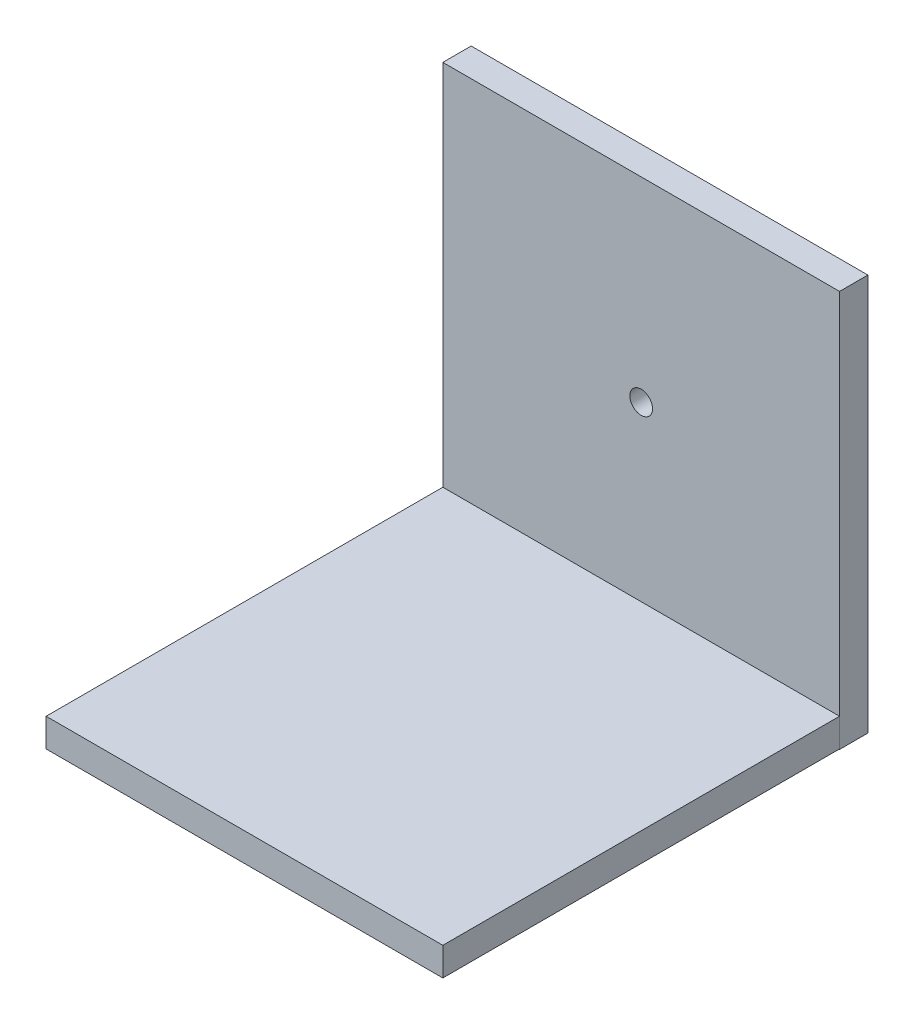
SolidWorks part; units mm, degrees
ref_plane "Front Plane" through (0, 0, 0) normal (0, 0, 1) x (1, 0, 0)
ref_plane "Top Plane" through (0, 0, 0) normal (0, 1, 0) x (1, 0, 0)
ref_plane "Right Plane" through (0, 0, 0) normal (1, 0, 0) x (0, 0, -1)
sketch "Sketch1" plane through (0, 0, 0) normal (0, 1, 0) x (1, 0, 0)
  line L1 (0, 0) -> (70, 0)
  line L2 (0, 0) -> (0, -70)
  line L3 (0, -70) -> (70, -70)
  line L4 (70, 0) -> (70, -70)
  dimension "D1" = 70
  dimension "D2" = 70
sketch "Sketch2" plane through (0, -5.0785, 0) normal (0, 0, 1) x (1, 0, 0)
  line L1 (0, 0) -> (70, 0)
  line L2 (0, 0) -> (0, 70)
  line L3 (0, 70) -> (70, 70)
  line L4 (70, 0) -> (70, 70)
  dimension "D1" = 70
  dimension "D2" = 70
extrude "Boss-Extrude1" add sketch "Sketch2" against normal blind 5
extrude "Boss-Extrude2" add sketch "Sketch1" against normal blind 5 separate body contours L2 L3 L4 L1
sketch "Sketch3" plane through (0, 0, -5) normal (0, 0, -1) x (-1, 0, 0)
  line L0 (-35, 64.9215) -> (-35, -5.0785) construction
  line L1 (-70, 64.9215) -> (0, 64.9215) construction
  line L2 (0, -5.0785) -> (-70, -5.0785) construction
sketch "Sketch4" plane through (0, -5, 0) normal (0, -1, 0) x (1, 0, 0)
  line L0 (35, 0) -> (35, 70) construction
  line L1 (0, 0) -> (70, 0) construction
  line L2 (0, 70) -> (70, 70) construction
sketch "Sketch5" plane through (0, 0, -5) normal (0, 0, -1) x (-1, 0, 0)
  line L0 (-35, -5.0785) -> (-35, 30.4775) construction
  circle A0 centre (-35, 30.4775) radius 2
extrude "Cut-Extrude1" cut sketch "Sketch5" against normal blind 5
